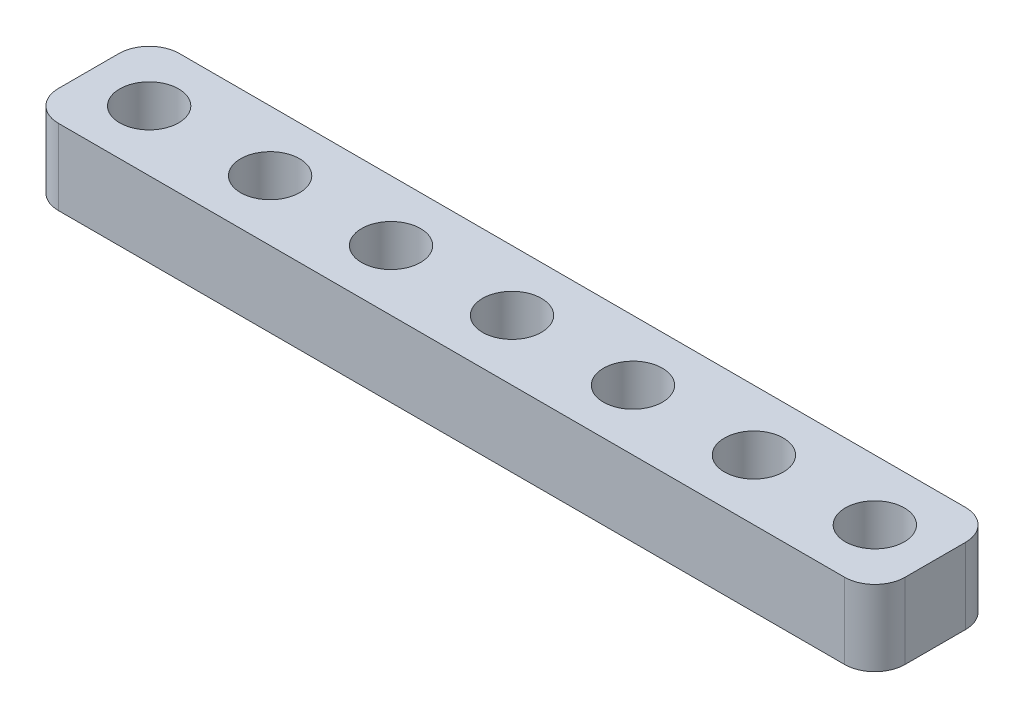
SolidWorks part; units mm, degrees
ref_plane "Front Plane" through (0, 0, 0) normal (0, 0, 1) x (1, 0, 0)
ref_plane "Top Plane" through (0, 0, 0) normal (0, 1, 0) x (1, 0, 0)
ref_plane "Right Plane" through (0, 0, 0) normal (1, 0, 0) x (0, 0, -1)
sketch "Sketch1" plane through (0, 0, 0) normal (0, 1, 0) x (1, 0, 0)
  line L1 (2, 0) -> (54, 0)
  line L2 (0, -2) -> (0, -6)
  line L3 (2, -8) -> (54, -8)
  line L4 (56, -2) -> (56, -6)
  arc A0 (54, -8) -> (56, -6) centre (54, -6) ccw
  arc A1 (0, -6) -> (2, -8) centre (2, -6) ccw
  arc A2 (2, 0) -> (0, -2) centre (2, -2) ccw
  arc A3 (54, 0) -> (56, -2) centre (54, -2) cw
  point P7 (56, -8)
  point P12 (0, 0)
  point P15 (56, 0)
  dimension "D3" = 2
  dimension "D1" = 56
  dimension "D2" = 8
extrude "Boss-Extrude1" add sketch "Sketch1" along normal blind 5
sketch "Sketch2" plane through (0, 5, 0) normal (0, 1, 0) x (1, 0, 0)
  line L0 (54, 0) -> (2, 0) construction
  line L1 (56, -6) -> (56, -2) construction
  line L2 (52, -4) -> (0, -4) construction
  line L3 (0, -2) -> (0, -6) construction
  circle A0 centre (52, -4) radius 1.95
  circle A1 centre (44, -4) radius 1.95
  circle A3 centre (-12, -4) radius 1.95
  circle A4 centre (-4, -4) radius 1.95
  circle A5 centre (4, -4) radius 1.95
  circle A6 centre (12, -4) radius 1.95
  circle A7 centre (20, -4) radius 1.95
  circle A8 centre (28, -4) radius 1.95
  circle A9 centre (36, -4) radius 1.95
  dimension "D1" = 3.9
  dimension "D4" = 3.9
  dimension "D8" = 3.9
  dimension "D9" = 3.9
  dimension "D10" = 3.9
  dimension "D11" = 3.9
  dimension "D12" = 3.9
  dimension "D13" = 3.9
  dimension "D14" = 3.9
  dimension "D2" = 4
  dimension "D3" = 4
  dimension "D5" = 8
  dimension "D15" = 8
  dimension "D16" = 8
  dimension "D17" = 8
  dimension "D18" = 8
  dimension "D19" = 8
  dimension "D20" = 8
  dimension "D21" = 8
extrude "Cut-Extrude1" cut sketch "Sketch2" against normal through all
